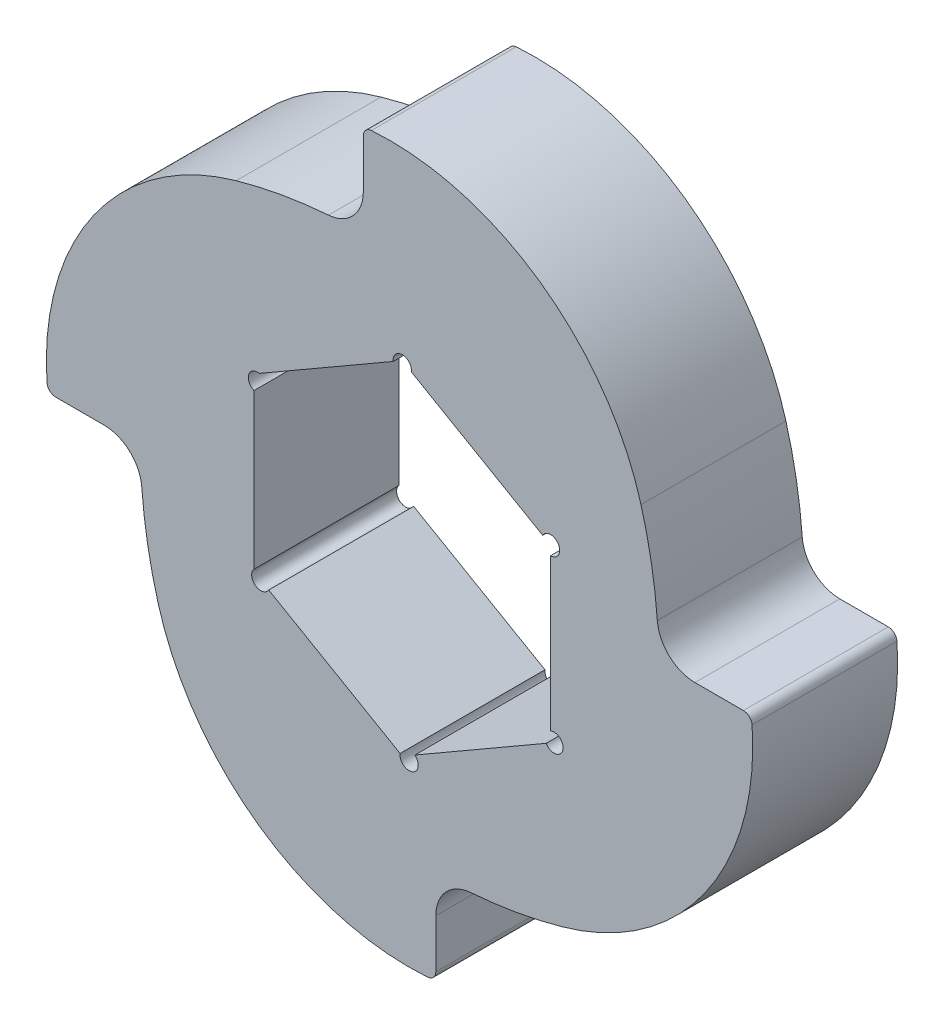
SolidWorks part; units mm, degrees
ref_plane "Front Plane" through (0, 0, 0) normal (0, 0, 1) x (1, 0, 0)
ref_plane "Top Plane" through (0, 0, 0) normal (0, 1, 0) x (1, 0, 0)
ref_plane "Right Plane" through (0, 0, 0) normal (1, 0, 0) x (0, 0, -1)
sketch "Sketch1" plane through (0, 0, 0) normal (0, 0, 1) x (1, 0, 0)
  circle A0 centre (0, 0) radius 16
  dimension "D1" = 32
extrude "Boss-Extrude1" add sketch "Sketch1" along normal blind 6.35
sketch "Sketch2" plane through (0, 0, 6.35) normal (0, 0, 1) x (1, 0, 0)
  line L4 (14.9493, 1.7008) -> (12.8238, 1.7008)
  line L5 (-1.7075, 15.1827) -> (-1.7075, 13.0571)
  line L6 (-15.1893, -1.4742) -> (-13.0638, -1.4742)
  line L7 (1.4675, -14.956) -> (1.4675, -12.8305)
  arc A16 (15.3294, 1.347) -> (14.9493, 1.7008) centre (14.9493, 1.3198) ccw
  arc A17 (11.1774, 3.2286) -> (12.8238, 1.7008) centre (12.8238, 3.3518) ccw
  arc A18 (11.1774, 3.2286) -> (10.4617, 7.2726) centre (-9.2386, 1.7008) ccw
  arc A19 (10.4617, 7.2726) -> (-1.3537, 15.5627) centre (-0.5368, 4.1619) ccw
  arc A20 (-1.3537, 15.5627) -> (-1.7075, 15.1827) centre (-1.3265, 15.1827) ccw
  arc A21 (-3.2353, 11.4107) -> (-1.7075, 13.0571) centre (-3.3585, 13.0571) ccw
  arc A22 (-3.2353, 11.4107) -> (-7.2793, 10.695) centre (-1.7075, -9.0053) ccw
  arc A23 (-7.2793, 10.695) -> (-15.5694, -1.1204) centre (-4.1686, -0.3035) ccw
  arc A24 (-15.5694, -1.1204) -> (-15.1893, -1.4742) centre (-15.1893, -1.0932) ccw
  arc A25 (-11.4174, -3.002) -> (-13.0638, -1.4742) centre (-13.0638, -3.1252) ccw
  arc A26 (-11.4174, -3.002) -> (-10.7017, -7.046) centre (8.9986, -1.4742) ccw
  arc A27 (-10.7017, -7.046) -> (1.1137, -15.3361) centre (0.2969, -3.9353) ccw
  arc A28 (1.1137, -15.3361) -> (1.4675, -14.956) centre (1.0865, -14.956) ccw
  arc A29 (2.9953, -11.1841) -> (1.4675, -12.8305) centre (3.1185, -12.8305) ccw
  arc A30 (2.9953, -11.1841) -> (7.0393, -10.4684) centre (1.4675, 9.232) ccw
  arc A31 (7.0393, -10.4684) -> (15.3294, 1.347) centre (3.9286, 0.5302) ccw
extrude "Cut-Extrude1" cut sketch "Sketch2" against normal through all flip side to cut
sketch "Sketch3" plane through (0, 0, 6.35) normal (0, 0, 1) x (1, 0, 0)
  line L0 (1.4675, -14.956) -> (1.4675, -12.8305) construction
  line L1 (0, 7.5056) -> (-6.5, 3.7528)
  line L2 (-6.5, 3.7528) -> (-6.5, -3.7528)
  line L3 (-6.5, -3.7528) -> (0, -7.5056)
  line L4 (0, -7.5056) -> (6.5, -3.7528)
  line L5 (6.5, -3.7528) -> (6.5, 3.7528)
  line L6 (6.5, 3.7528) -> (0, 7.5056)
  line L7 (-1.7075, 15.1827) -> (-1.7075, 13.0571) construction
  circle A0 centre (0, 0) radius 6.5 construction
  dimension "D1" = 13
  dimension "D2" = 5.0325
  dimension "D3" = 4.7925
extrude "Cut-Extrude2" cut sketch "Sketch3" against normal through all
sketch "Sketch4" plane through (0, 0, 0) normal (0, 0, -1) x (-1, 0, 0)
  circle A0 centre (-6.5, 3.7528) radius 0.4
  circle A1 centre (0, 7.3323) radius 0.4
  circle A2 centre (6.35, 3.493) radius 0.4
  circle A3 centre (6.2, -3.926) radius 0.4
  circle A4 centre (-0.3, -7.5056) radius 0.4
  circle A5 centre (-6.65, -3.6662) radius 0.4
  point P16 (-0.15, -0.0866)
  dimension "D1" = 6
extrude "Cut-Extrude3" cut sketch "Sketch4" against normal up to next
